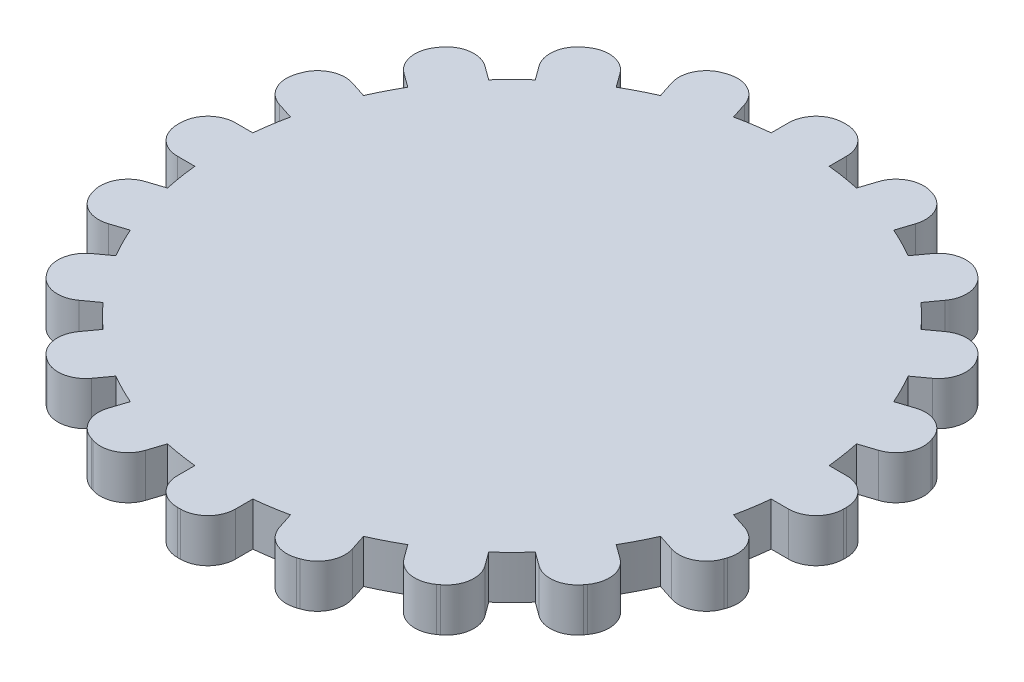
SolidWorks part; units mm, degrees
ref_plane "Front Plane" through (0, 0, 0) normal (0, 0, 1) x (1, 0, 0)
ref_plane "Top Plane" through (0, 0, 0) normal (0, 1, 0) x (1, 0, 0)
ref_plane "Right Plane" through (0, 0, 0) normal (1, 0, 0) x (0, 0, -1)
sketch "Sketch1" plane through (0, 0, 0) normal (0, 1, 0) x (1, 0, 0)
  line L0 (0, -10) -> (0, -1.5)
  line L50 (0, 1.5) -> (0, 10)
  line L51 (-2.5, -1.5) -> (2.5, -1.5)
  line L52 (-13, 0) -> (13, 0)
  line L53 (-13, -0.1) -> (-13, 0.1)
  line L54 (-11.1, 2) -> (-9.798, 2)
  line L55 (-11.1, -2) -> (-9.798, -2)
  line L56 (-2.5, -1.5) -> (-2.5, 1.5)
  line L57 (-7.8045, 8.1425) -> (-6.7511, 7.3771)
  line L58 (-10.576, 7.5603) -> (-10.4584, 7.7221)
  line L59 (-10.1557, 4.9064) -> (-9.1023, 4.1411)
  line L60 (-1.528, 11.1748) -> (-1.1256, 9.9364)
  line L61 (-4.1123, 12.3328) -> (-3.9221, 12.3946)
  line L62 (-5.3322, 9.9387) -> (-4.9298, 8.7004)
  line L63 (5.3322, 9.9387) -> (4.9298, 8.7004)
  line L64 (3.9221, 12.3946) -> (4.1123, 12.3328)
  line L65 (1.528, 11.1748) -> (1.1256, 9.9364)
  line L66 (10.1557, 4.9064) -> (9.1023, 4.1411)
  line L67 (10.4584, 7.7221) -> (10.576, 7.5603)
  line L68 (7.8045, 8.1425) -> (6.7511, 7.3771)
  line L69 (11.1, -2) -> (9.798, -2)
  line L70 (13, 0.1) -> (13, -0.1)
  line L71 (11.1, 2) -> (9.798, 2)
  line L72 (7.8045, -8.1425) -> (6.7511, -7.3771)
  line L73 (10.576, -7.5603) -> (10.4584, -7.7221)
  line L74 (10.1557, -4.9064) -> (9.1023, -4.1411)
  line L75 (1.528, -11.1748) -> (1.1256, -9.9364)
  line L76 (4.1123, -12.3328) -> (3.9221, -12.3946)
  line L77 (5.3322, -9.9387) -> (4.9298, -8.7004)
  line L78 (-5.3322, -9.9387) -> (-4.9298, -8.7004)
  line L79 (-3.9221, -12.3946) -> (-4.1123, -12.3328)
  line L80 (-1.528, -11.1748) -> (-1.1256, -9.9364)
  line L81 (-10.1557, -4.9064) -> (-9.1023, -4.1411)
  line L82 (-10.4584, -7.7221) -> (-10.576, -7.5603)
  line L83 (-7.8045, -8.1425) -> (-6.7511, -7.3771)
  line L84 (-2.5, 1.5) -> (2.5, 1.5)
  line L85 (2.5, -1.5) -> (2.5, 1.5)
  line L86 (-2.5, -1.5) -> (2.5, 1.5) construction
  line L87 (-2.5, 1.5) -> (2.5, -1.5) construction
  arc A13 (-9.1023, 4.1411) -> (-9.798, 2) centre (0, 0) ccw
  arc A14 (-13, 0.1) -> (-11.1, 2) centre (-11.1, 0.1) cw
  arc A15 (-13, -0.1) -> (-11.1, -2) centre (-11.1, -0.1) ccw
  arc A16 (-10.4584, 7.7221) -> (-7.8045, 8.1425) centre (-8.9213, 6.6053) cw
  arc A17 (-10.576, 7.5603) -> (-10.1557, 4.9064) centre (-9.0389, 6.4435) ccw
  arc A18 (-3.9221, 12.3946) -> (-1.528, 11.1748) centre (-3.335, 10.5876) cw
  arc A19 (-4.1123, 12.3328) -> (-5.3322, 9.9387) centre (-3.5252, 10.5258) ccw
  arc A20 (4.1123, 12.3328) -> (5.3322, 9.9387) centre (3.5252, 10.5258) cw
  arc A21 (3.9221, 12.3946) -> (1.528, 11.1748) centre (3.335, 10.5876) ccw
  arc A22 (10.576, 7.5603) -> (10.1557, 4.9064) centre (9.0389, 6.4435) cw
  arc A23 (10.4584, 7.7221) -> (7.8045, 8.1425) centre (8.9213, 6.6053) ccw
  arc A24 (13, -0.1) -> (11.1, -2) centre (11.1, -0.1) cw
  arc A25 (13, 0.1) -> (11.1, 2) centre (11.1, 0.1) ccw
  arc A26 (10.4584, -7.7221) -> (7.8045, -8.1425) centre (8.9213, -6.6053) cw
  arc A27 (10.576, -7.5603) -> (10.1557, -4.9064) centre (9.0389, -6.4435) ccw
  arc A28 (3.9221, -12.3946) -> (1.528, -11.1748) centre (3.335, -10.5876) cw
  arc A29 (4.1123, -12.3328) -> (5.3322, -9.9387) centre (3.5252, -10.5258) ccw
  arc A30 (-4.1123, -12.3328) -> (-5.3322, -9.9387) centre (-3.5252, -10.5258) cw
  arc A31 (-3.9221, -12.3946) -> (-1.528, -11.1748) centre (-3.335, -10.5876) ccw
  arc A32 (-10.576, -7.5603) -> (-10.1557, -4.9064) centre (-9.0389, -6.4435) cw
  arc A33 (-10.4584, -7.7221) -> (-7.8045, -8.1425) centre (-8.9213, -6.6053) ccw
  arc A34 (-4.9298, 8.7004) -> (-6.7511, 7.3771) centre (0, 0) ccw
  arc A35 (1.1256, 9.9364) -> (-1.1256, 9.9364) centre (0, 0) ccw
  arc A36 (6.7511, 7.3771) -> (4.9298, 8.7004) centre (0, 0) ccw
  arc A37 (9.798, 2) -> (9.1023, 4.1411) centre (0, 0) ccw
  arc A38 (9.1023, -4.1411) -> (9.798, -2) centre (0, 0) ccw
  arc A39 (4.9298, -8.7004) -> (6.7511, -7.3771) centre (0, 0) ccw
  arc A40 (-1.1256, -9.9364) -> (1.1256, -9.9364) centre (0, 0) ccw
  arc A41 (-6.7511, -7.3771) -> (-4.9298, -8.7004) centre (0, 0) ccw
  arc A42 (-9.798, -2) -> (-9.1023, -4.1411) centre (0, 0) ccw
  point P6 (0, 0)
  point P8 (0, 0)
  point P9 (0, 0)
  point P17 (0, 0)
  point P18 (0, 0)
  point P22 (-13, 2)
  point P63 (0, 0)
  point P119 (0, 0)
  dimension "D1" = 20
  dimension "D2" = 26
  dimension "D4" = 1.9
  dimension "D3" = 2
  dimension "D5" = 10
  dimension "D6" = 3
  dimension "D7" = 5
extrude "Boss-Extrude1" add sketch "Sketch1" along normal blind 3 contours L71 A37 L66 A22 L67 A23 L68 A36 L63 A20 L64 A21 L65 A35 L50 L84 L85 L52 L70 A25 | L50 A35 L60 A18 L61 A19 L62 A34 L57 A16 L58 A17 L59 A13 L54 A14 L53 L52 L56 L84 | L55 A42 L81 A32 L82 A33 L83 A41 L78 A30 L79 A31 L80 A40 L0 L51 L56 L52 L53 A15 | L0 A40 L75 A28 L76 A29 L77 A39 L72 A26 L73 A27 L74 A38 L69 A24 L70 L52 L85 L51
sketch "Sketch2" plane through (0, 0, 0) normal (0, 1, 0) x (1, 0, 0)
  line L0 (-2, 0) -> (2, 0)
  line L1 (-23, -0.1) -> (-23, 0.1)
  line L2 (-21.1, 2) -> (-19.8997, 2)
  line L3 (-21.1, -2) -> (-19.8997, -2)
  line L4 (-20.6853, 4.6181) -> (-19.5438, 4.2472)
  line L5 (-19.4493, 8.4224) -> (-18.3078, 8.0515)
  line L6 (-21.9052, 7.0123) -> (-21.8434, 7.2025)
  line L7 (-18.2458, 10.7842) -> (-17.2748, 10.0787)
  line L8 (-15.8947, 14.0203) -> (-14.9237, 13.3148)
  line L9 (-18.6662, 13.4382) -> (-18.5486, 13.6)
  line L10 (-14.0203, 15.8947) -> (-13.3148, 14.9237)
  line L11 (-10.7842, 18.2458) -> (-10.0787, 17.2748)
  line L12 (-13.6, 18.5486) -> (-13.4382, 18.6662)
  line L13 (-8.4224, 19.4493) -> (-8.0515, 18.3078)
  line L14 (-4.6181, 20.6853) -> (-4.2472, 19.5438)
  line L15 (-7.2025, 21.8434) -> (-7.0123, 21.9052)
  line L16 (-2, 21.1) -> (-2, 19.8997)
  line L17 (2, 21.1) -> (2, 19.8997)
  line L18 (-0.1, 23) -> (0.1, 23)
  line L19 (4.6181, 20.6853) -> (4.2472, 19.5438)
  line L20 (8.4224, 19.4493) -> (8.0515, 18.3078)
  line L21 (7.0123, 21.9052) -> (7.2025, 21.8434)
  line L22 (10.7842, 18.2458) -> (10.0787, 17.2748)
  line L23 (14.0203, 15.8947) -> (13.3148, 14.9237)
  line L24 (13.4382, 18.6662) -> (13.6, 18.5486)
  line L25 (15.8947, 14.0203) -> (14.9237, 13.3148)
  line L26 (18.2458, 10.7842) -> (17.2748, 10.0787)
  line L27 (18.5486, 13.6) -> (18.6662, 13.4382)
  line L28 (19.4493, 8.4224) -> (18.3078, 8.0515)
  line L29 (20.6853, 4.6181) -> (19.5438, 4.2472)
  line L30 (21.8434, 7.2025) -> (21.9052, 7.0123)
  line L31 (21.1, 2) -> (19.8997, 2)
  line L32 (21.1, -2) -> (19.8997, -2)
  line L33 (23, 0.1) -> (23, -0.1)
  line L34 (20.6853, -4.6181) -> (19.5438, -4.2472)
  line L35 (19.4493, -8.4224) -> (18.3078, -8.0515)
  line L36 (21.9052, -7.0123) -> (21.8434, -7.2025)
  line L37 (18.2458, -10.7842) -> (17.2748, -10.0787)
  line L38 (15.8947, -14.0203) -> (14.9237, -13.3148)
  line L39 (18.6662, -13.4382) -> (18.5486, -13.6)
  line L40 (14.0203, -15.8947) -> (13.3148, -14.9237)
  line L41 (10.7842, -18.2458) -> (10.0787, -17.2748)
  line L42 (13.6, -18.5486) -> (13.4382, -18.6662)
  line L43 (8.4224, -19.4493) -> (8.0515, -18.3078)
  line L44 (4.6181, -20.6853) -> (4.2472, -19.5438)
  line L45 (7.2025, -21.8434) -> (7.0123, -21.9052)
  line L46 (2, -21.1) -> (2, -19.8997)
  line L47 (-2, -21.1) -> (-2, -19.8997)
  line L48 (0.1, -23) -> (-0.1, -23)
  line L49 (-4.6181, -20.6853) -> (-4.2472, -19.5438)
  line L50 (-8.4224, -19.4493) -> (-8.0515, -18.3078)
  line L51 (-7.0123, -21.9052) -> (-7.2025, -21.8434)
  line L52 (-10.7842, -18.2458) -> (-10.0787, -17.2748)
  line L53 (-14.0203, -15.8947) -> (-13.3148, -14.9237)
  line L54 (-13.4382, -18.6662) -> (-13.6, -18.5486)
  line L55 (-15.8947, -14.0203) -> (-14.9237, -13.3148)
  line L56 (-18.2458, -10.7842) -> (-17.2748, -10.0787)
  line L57 (-18.5486, -13.6) -> (-18.6662, -13.4382)
  line L58 (-19.4493, -8.4224) -> (-18.3078, -8.0515)
  line L59 (-20.6853, -4.6181) -> (-19.5438, -4.2472)
  line L60 (-21.8434, -7.2025) -> (-21.9052, -7.0123)
  arc A0 (-18.3078, -8.0515) -> (-17.2748, -10.0787) centre (0, 0) ccw
  arc A1 (-21.1, 2) -> (-23, 0.1) centre (-21.1, 0.1) ccw
  arc A2 (-21.1, -2) -> (-23, -0.1) centre (-21.1, -0.1) cw
  arc A3 (-20.6853, 4.6181) -> (-21.9052, 7.0123) centre (-20.0982, 6.4252) cw
  arc A4 (-19.4493, 8.4224) -> (-21.8434, 7.2025) centre (-20.0364, 6.6154) ccw
  arc A5 (-18.2458, 10.7842) -> (-18.6662, 13.4382) centre (-17.129, 12.3214) cw
  arc A6 (-15.8947, 14.0203) -> (-18.5486, 13.6) centre (-17.0115, 12.4832) ccw
  arc A7 (-14.0203, 15.8947) -> (-13.6, 18.5486) centre (-12.4832, 17.0115) cw
  arc A8 (-10.7842, 18.2458) -> (-13.4382, 18.6662) centre (-12.3214, 17.129) ccw
  arc A9 (-8.4224, 19.4493) -> (-7.2025, 21.8434) centre (-6.6154, 20.0364) cw
  arc A10 (-4.6181, 20.6853) -> (-7.0123, 21.9052) centre (-6.4252, 20.0982) ccw
  arc A11 (-2, 21.1) -> (-0.1, 23) centre (-0.1, 21.1) cw
  arc A12 (2, 21.1) -> (0.1, 23) centre (0.1, 21.1) ccw
  arc A13 (4.6181, 20.6853) -> (7.0123, 21.9052) centre (6.4252, 20.0982) cw
  arc A14 (8.4224, 19.4493) -> (7.2025, 21.8434) centre (6.6154, 20.0364) ccw
  arc A15 (10.7842, 18.2458) -> (13.4382, 18.6662) centre (12.3214, 17.129) cw
  arc A16 (14.0203, 15.8947) -> (13.6, 18.5486) centre (12.4832, 17.0115) ccw
  arc A17 (15.8947, 14.0203) -> (18.5486, 13.6) centre (17.0115, 12.4832) cw
  arc A18 (18.2458, 10.7842) -> (18.6662, 13.4382) centre (17.129, 12.3214) ccw
  arc A19 (19.4493, 8.4224) -> (21.8434, 7.2025) centre (20.0364, 6.6154) cw
  arc A20 (20.6853, 4.6181) -> (21.9052, 7.0123) centre (20.0982, 6.4252) ccw
  arc A21 (21.1, 2) -> (23, 0.1) centre (21.1, 0.1) cw
  arc A22 (21.1, -2) -> (23, -0.1) centre (21.1, -0.1) ccw
  arc A23 (20.6853, -4.6181) -> (21.9052, -7.0123) centre (20.0982, -6.4252) cw
  arc A24 (19.4493, -8.4224) -> (21.8434, -7.2025) centre (20.0364, -6.6154) ccw
  arc A25 (18.2458, -10.7842) -> (18.6662, -13.4382) centre (17.129, -12.3214) cw
  arc A26 (15.8947, -14.0203) -> (18.5486, -13.6) centre (17.0115, -12.4832) ccw
  arc A27 (14.0203, -15.8947) -> (13.6, -18.5486) centre (12.4832, -17.0115) cw
  arc A28 (10.7842, -18.2458) -> (13.4382, -18.6662) centre (12.3214, -17.129) ccw
  arc A29 (8.4224, -19.4493) -> (7.2025, -21.8434) centre (6.6154, -20.0364) cw
  arc A30 (4.6181, -20.6853) -> (7.0123, -21.9052) centre (6.4252, -20.0982) ccw
  arc A31 (2, -21.1) -> (0.1, -23) centre (0.1, -21.1) cw
  arc A32 (-2, -21.1) -> (-0.1, -23) centre (-0.1, -21.1) ccw
  arc A33 (-4.6181, -20.6853) -> (-7.0123, -21.9052) centre (-6.4252, -20.0982) cw
  arc A34 (-8.4224, -19.4493) -> (-7.2025, -21.8434) centre (-6.6154, -20.0364) ccw
  arc A35 (-10.7842, -18.2458) -> (-13.4382, -18.6662) centre (-12.3214, -17.129) cw
  arc A36 (-14.0203, -15.8947) -> (-13.6, -18.5486) centre (-12.4832, -17.0115) ccw
  arc A37 (-15.8947, -14.0203) -> (-18.5486, -13.6) centre (-17.0115, -12.4832) cw
  arc A38 (-18.2458, -10.7842) -> (-18.6662, -13.4382) centre (-17.129, -12.3214) ccw
  arc A39 (-19.4493, -8.4224) -> (-21.8434, -7.2025) centre (-20.0364, -6.6154) cw
  arc A40 (-20.6853, -4.6181) -> (-21.9052, -7.0123) centre (-20.0982, -6.4252) ccw
  arc A41 (-19.8997, -2) -> (-19.5438, -4.2472) centre (0, 0) ccw
  arc A42 (-19.5438, 4.2472) -> (-19.8997, 2) centre (0, 0) ccw
  arc A43 (-17.2748, 10.0787) -> (-18.3078, 8.0515) centre (0, 0) ccw
  arc A44 (-13.3148, 14.9237) -> (-14.9237, 13.3148) centre (0, 0) ccw
  arc A45 (-8.0515, 18.3078) -> (-10.0787, 17.2748) centre (0, 0) ccw
  arc A46 (-2, 19.8997) -> (-4.2472, 19.5438) centre (0, 0) ccw
  arc A47 (4.2472, 19.5438) -> (2, 19.8997) centre (0, 0) ccw
  arc A48 (10.0787, 17.2748) -> (8.0515, 18.3078) centre (0, 0) ccw
  arc A49 (14.9237, 13.3148) -> (13.3148, 14.9237) centre (0, 0) ccw
  arc A50 (18.3078, 8.0515) -> (17.2748, 10.0787) centre (0, 0) ccw
  arc A51 (19.8997, 2) -> (19.5438, 4.2472) centre (0, 0) ccw
  arc A52 (19.5438, -4.2472) -> (19.8997, -2) centre (0, 0) ccw
  arc A53 (17.2748, -10.0787) -> (18.3078, -8.0515) centre (0, 0) ccw
  arc A54 (13.3148, -14.9237) -> (14.9237, -13.3148) centre (0, 0) ccw
  arc A55 (8.0515, -18.3078) -> (10.0787, -17.2748) centre (0, 0) ccw
  arc A56 (2, -19.8997) -> (4.2472, -19.5438) centre (0, 0) ccw
  arc A57 (-10.0787, -17.2748) -> (-8.0515, -18.3078) centre (0, 0) ccw
  arc A58 (-4.2472, -19.5438) -> (-2, -19.8997) centre (0, 0) ccw
  arc A59 (-14.9237, -13.3148) -> (-13.3148, -14.9237) centre (0, 0) ccw
  point P6 (0, 0)
  point P10 (-23, 2)
  point P170 (0, 0)
  dimension "D1" = 40
  dimension "D4" = 1.9
  dimension "D5" = 20
extrude "Boss-Extrude2" add sketch "Sketch2" along normal blind 3
